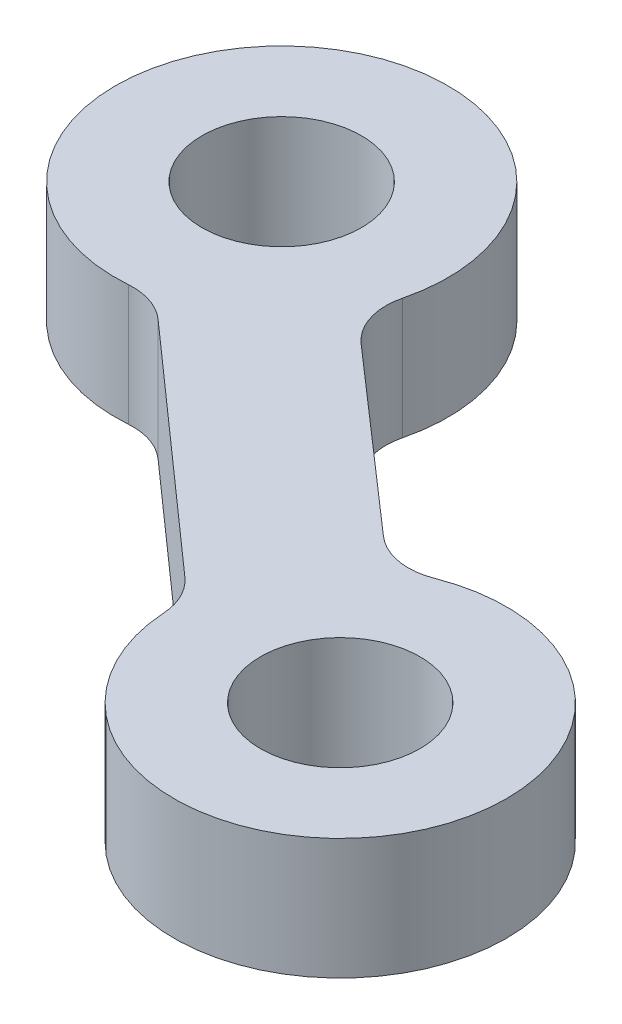
SolidWorks part; units mm, degrees
material "PLA"
ref_plane "Front Plane" through (0, 0, 0) normal (0, 0, 1) x (1, 0, 0)
ref_plane "Top Plane" through (0, 0, 0) normal (0, 1, 0) x (1, 0, 0)
ref_plane "Right Plane" through (0, 0, 0) normal (1, 0, 0) x (0, 0, -1)
ref_plane "Plane1" through (0, 0, 0) normal (0, -1, 0) x (1, 0, 0)
sketch "Sketch1" plane through (0, 0, 0) normal (0, -1, 0) x (1, 0, 0)
  line L0 (91.8288, -34.6042) -> (83.9878, -41.5566)
  line L1 (88.0534, -44.2079) -> (93.9375, -39.0622)
  arc A0 (92.498, -33.2346) -> (91.8288, -34.6042) centre (90.502, -33.1077) cw
  arc A1 (83.9878, -41.5566) -> (82.5102, -42.0544) centre (82.6609, -40.0601) cw
  arc A2 (82.5102, -42.0544) -> (87.4302, -46.2002) centre (82.0956, -47.5388) ccw
  arc A3 (87.4302, -46.2002) -> (88.0534, -44.2079) centre (89.37, -45.7134) cw
  arc A4 (93.9375, -39.0622) -> (95.9828, -38.7052) centre (95.2541, -40.5678) cw
  arc A5 (95.9828, -38.7052) -> (92.498, -33.2346) centre (97.9869, -33.5834) ccw
  circle A6 centre (82.0956, -47.5388) radius 2.6375
  circle A7 centre (97.9869, -33.5834) radius 2.6375
extrude "Boss-Extrude1" add sketch "Sketch1" against normal blind 4
